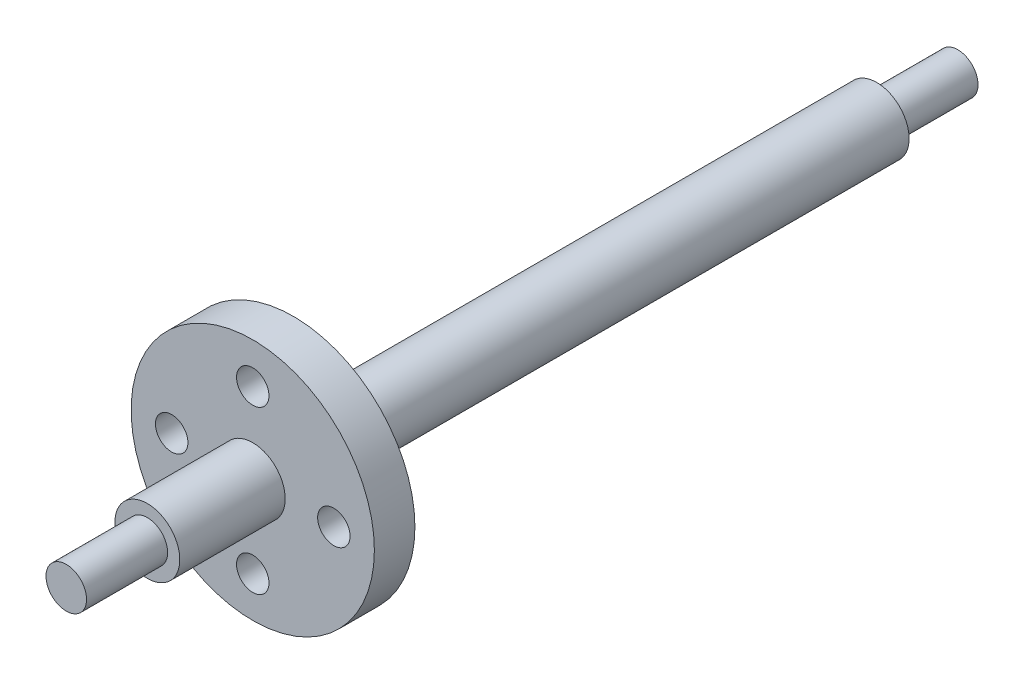
SolidWorks part; units mm, degrees
material "6061 Alloy"
ref_plane "Front Plane" through (0, 0, 0) normal (0, 0, 1) x (1, 0, 0)
ref_plane "Top Plane" through (0, 0, 0) normal (0, 1, 0) x (1, 0, 0)
ref_plane "Right Plane" through (0, 0, 0) normal (1, 0, 0) x (0, 0, -1)
sketch "Sketch1" plane through (0, 0, 0) normal (0, 0, 1) x (1, 0, 0)
  circle A0 centre (0, 0) radius 4
  dimension "D1" = 8
extrude "Boss-Extrude1" add sketch "Sketch1" along normal blind 109.95
other "Freeze***"
ref_plane "Plane1" through (0, 0, 54.975) normal (0, 0, 1) x (1, 0, 0)
sketch "Sketch2" plane through (0, 0, 0) normal (0, 0, -1) x (-1, 0, 0)
  circle A0 centre (0, 0) radius 2.5
  circle A1 centre (0, 0) radius 4
  circle A2 centre (0, 0) radius 4 construction
  dimension "D1" = 5
extrude "Cut-Extrude1" cut sketch "Sketch2" against normal blind 10
mirror "Mirror1" about plane through (0, 0, 54.975) normal (0, 0, 1) of "Cut-Extrude1"
ref_plane "Plane2" through (0, 0, 81.95) normal (0, 0, 1) x (1, 0, 0)
sketch "Sketch3" plane through (0, 0, 81.95) normal (0, 0, 1) x (1, 0, 0)
  circle A0 centre (0, 0) radius 15
  circle A1 centre (0, 0) radius 10 construction
  circle A2 centre (0, 10) radius 2
  circle A3 centre (10, 0) radius 2
  circle A4 centre (0, -10) radius 2
  circle A5 centre (-10, 0) radius 2
  point P15 (0, 0)
  dimension "D1" = 20
  dimension "D2" = 30
  dimension "D3" = 4
  dimension "D4" = 4
extrude "Boss-Extrude2" add sketch "Sketch3" along normal blind 5
